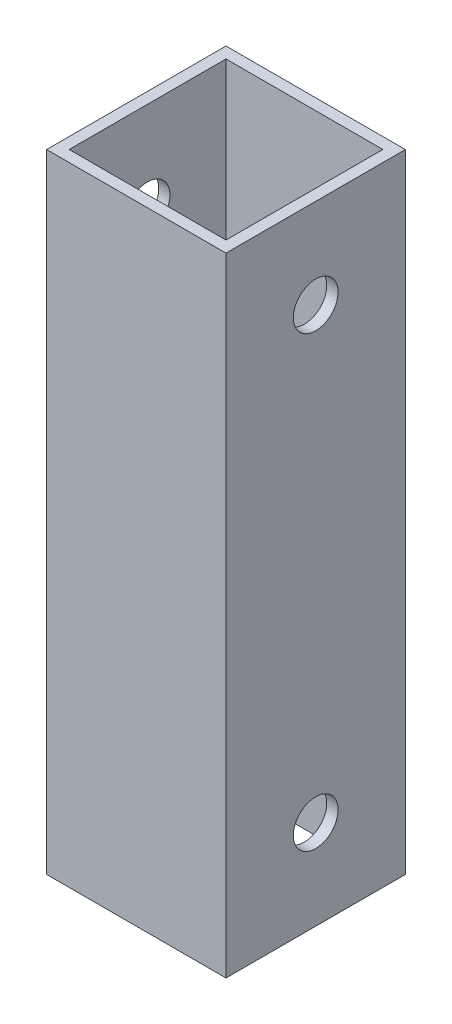
SolidWorks part; units mm, degrees
material "6061 Alloy"
ref_plane "Front Plane" through (0, 0, 0) normal (0, 0, 1) x (1, 0, 0)
ref_plane "Top Plane" through (0, 0, 0) normal (0, 1, 0) x (1, 0, 0)
ref_plane "Right Plane" through (0, 0, 0) normal (1, 0, 0) x (0, 0, -1)
sketch "Sketch1" plane through (0, 0, 0) normal (0, 1, 0) x (1, 0, 0)
  line L0 (-25.4, -25.4) -> (25.4, 25.4) construction
  line L1 (-25.4, 25.4) -> (25.4, 25.4)
  line L2 (-25.4, 25.4) -> (-25.4, -25.4)
  line L3 (-25.4, -25.4) -> (25.4, -25.4)
  line L4 (25.4, 25.4) -> (25.4, -25.4)
  line L5 (22.225, -22.225) -> (-22.225, 22.225) construction
  line L6 (-22.225, 22.225) -> (22.1918, 22.225)
  line L7 (-22.225, 22.225) -> (-22.225, -22.1918)
  line L8 (-22.225, -22.1918) -> (22.1918, -22.1918)
  line L9 (22.1918, 22.225) -> (22.1918, -22.1918)
  point P7 (0, 0)
  point P10 (0, 0)
  point P14 (0, 0)
  dimension "D1" = 50.8
  dimension "D2" = 3.175
  dimension "D3" = 3.175
extrude "Boss-Extrude1" add sketch "Sketch1" along normal blind 177.8
sketch "Sketch2" plane through (-25.4, 0, 0) normal (-1, 0, 0) x (0, 0, 1)
  line L0 (25.4, 88.9) -> (-25.4, 88.9) construction
  line L1 (25.4, 177.8) -> (25.4, 0) construction
  line L2 (-25.4, 177.8) -> (-25.4, 0) construction
  line L4 (0, 152.4) -> (0, 25.4) construction
  circle A1 centre (0, 25.4) radius 6.35
  circle A2 centre (0, 152.4) radius 6.35
  point P6 (0, 0)
  point P7 (0, 0)
  point P10 (0, 88.9)
  point P13 (0, 88.9)
  dimension "D2" = 12.7
extrude "Cut-Extrude1" cut sketch "Sketch2" against normal through all
equation "\"D1@Boss-Extrude1\"=\"HoleDist\"+2"
